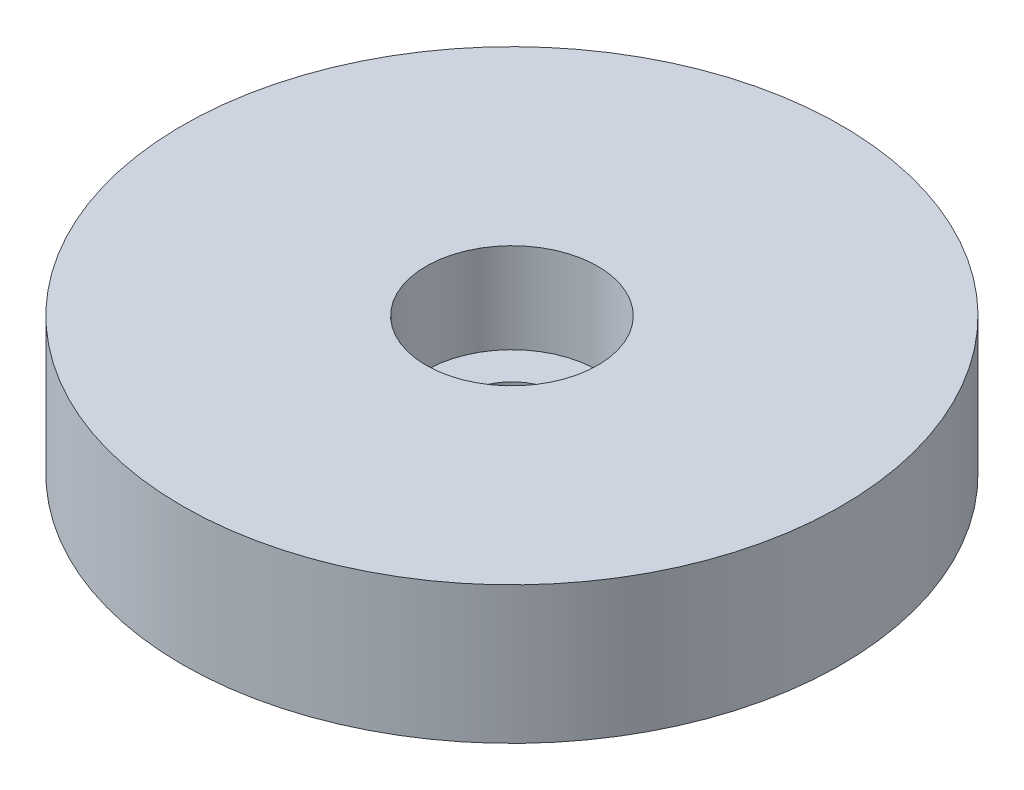
SolidWorks part; units mm, degrees
material "6061-T6 (SS)"
ref_plane "Front" through (0, 0, 0) normal (0, 0, 1) x (1, 0, 0)
ref_plane "Top" through (0, 0, 0) normal (0, 1, 0) x (1, 0, 0)
ref_plane "Right" through (0, 0, 0) normal (1, 0, 0) x (0, 0, -1)
sketch "Sketch1" plane through (0, 0, 0) normal (0, 1, 0) x (1, 0, 0)
  circle A0 centre (0, 0) radius 15.24
  dimension "D1" = 30.48
extrude "Extrude1" add sketch "Sketch1" along normal blind 6.35
sketch "Sketch3" plane through (0, 6.35, 0) normal (0, 1, 0) x (1, 0, 0)
  point P0 (0, 0)
hole_wizard "CBORE for #8 Socket Head Cap Screw1" positions "3DSketch1" profile "Sketch2" counterbore size "#8" standard "Ansi Inch" end condition up to next
sketch3d "3DSketch1"
  point P0 (0, 6.35, 0)
sketch "Sketch2" plane through (0, 6.35, 0) normal (1, 0, 0) x (0, 0, 1)
  line L0 (0, 0) -> (0, 6.35)
  line L1 (0, 6.35) -> (2.1526, 6.35)
  line L3 (2.1526, 6.35) -> (2.1526, 4.1656)
  line L4 (2.1526, 4.1656) -> (3.9687, 4.1656)
  line L5 (3.9687, 4.1656) -> (3.9688, 0)
  line L7 (3.9688, 0) -> (0, 0)
  line L11 (0, -6.35) -> (0, 107.95) construction
  dimension "Thru Hole Dia." = 4.3053
  dimension "Thru Hole Depth" = 6.35
  dimension "C'Bore Dia." = 7.9375
  dimension "C'Bore Depth" = 4.1656
